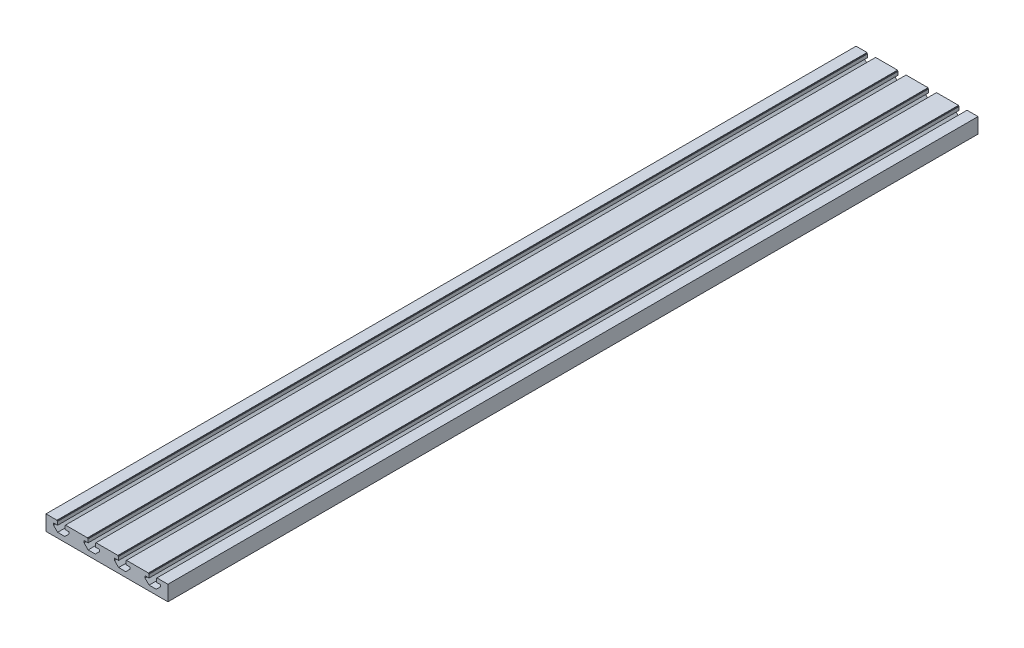
SolidWorks part; units mm, degrees
material "7079 Alloy"
ref_plane "Front" through (0, 0, 0) normal (0, 0, 1) x (1, 0, 0)
ref_plane "Top" through (0, 0, 0) normal (0, 1, 0) x (1, 0, 0)
ref_plane "Right" through (0, 0, 0) normal (1, 0, 0) x (0, 0, -1)
sketch "Sketch1" plane through (0, 0, 0) normal (0, 0, 1) x (1, 0, 0)
  line L0 (0, 22.5) -> (16.2, 22.5)
  line L1 (0, 0) -> (45, 0)
  line L2 (0, 0) -> (0, 22.5)
  line L3 (28.8, 22.5) -> (45, 22.5)
  line L7 (16.2, 22.5) -> (16.2, 21.5)
  line L8 (16.2, 21.5) -> (17.2, 21.5)
  line L9 (45, 22.5) -> (45, 0)
  line L10 (17.2, 21.5) -> (17.2, 16.5)
  line L11 (17.2, 16.5) -> (11.2, 16.5)
  line L12 (11.2, 16.5) -> (11.2, 13.5)
  line L13 (11.2, 13.5) -> (17.2, 7.5)
  line L14 (17.2, 7.5) -> (27.8, 7.5)
  line L15 (28.8, 22.5) -> (28.8, 21.5)
  line L16 (28.8, 21.5) -> (27.8, 21.5)
  line L17 (27.8, 21.5) -> (27.8, 16.5)
  line L18 (27.8, 16.5) -> (33.8, 16.5)
  line L19 (33.8, 16.5) -> (33.8, 13.5)
  line L20 (33.8, 13.5) -> (27.8, 7.5)
  dimension "D2" = 22.5
  dimension "D5" = 1
  dimension "D7" = 5
  dimension "D8" = 6
  dimension "D9" = 3
extrude "Extrude1" add sketch "Sketch1" along normal blind 1196
pattern_linear "LPattern2" count 4 spacing 45 along (1, 0, 0) of "Extrude1"
